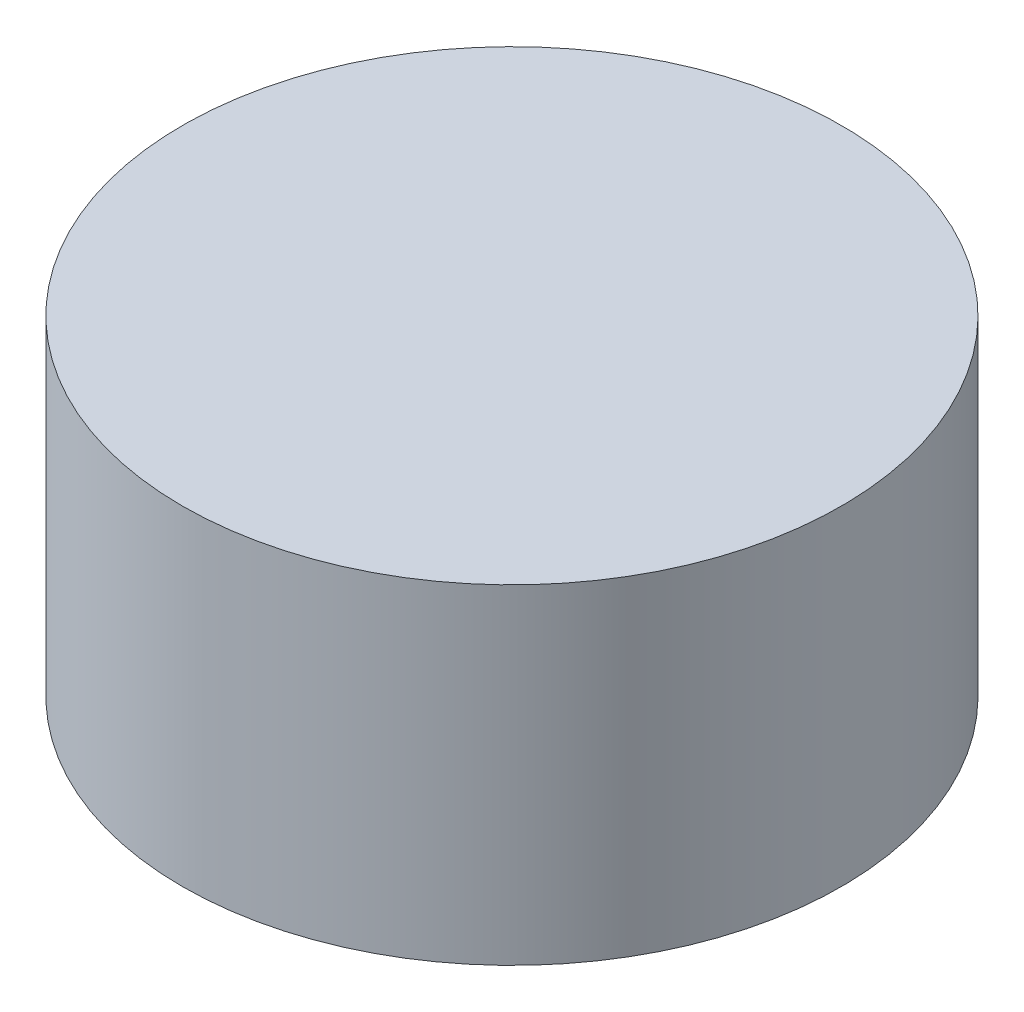
SolidWorks part; units mm, degrees
ref_plane "Front Plane" through (0, 0, 0) normal (0, 0, 1) x (1, 0, 0)
ref_plane "Top Plane" through (0, 0, 0) normal (0, 1, 0) x (1, 0, 0)
ref_plane "Right Plane" through (0, 0, 0) normal (1, 0, 0) x (0, 0, -1)
sketch "Sketch1" plane through (0, 0, 0) normal (0, 1, 0) x (1, 0, 0)
  circle A0 centre (0, 0) radius 10
  dimension "D1" = 20
extrude "Boss-Extrude1" add sketch "Sketch1" along normal blind 10
